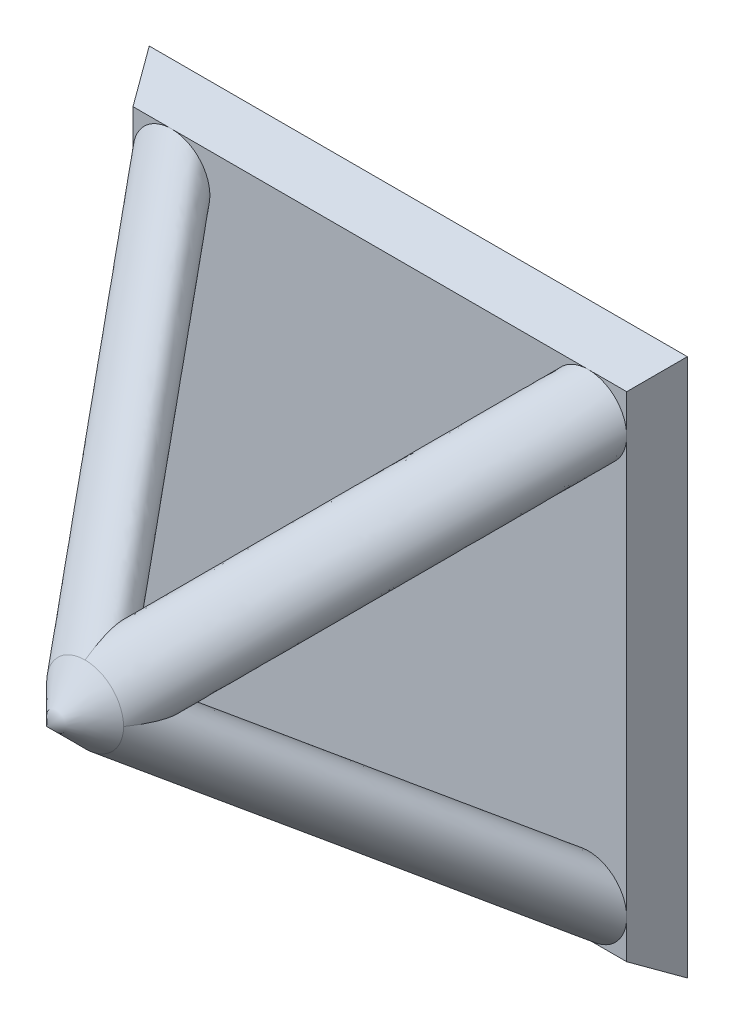
SolidWorks part; units mm, degrees
ref_plane "Front" through (0, 0, 0) normal (0, 0, 1) x (1, 0, 0)
ref_plane "Top" through (0, 0, 0) normal (0, 1, 0) x (1, 0, 0)
ref_plane "Right" through (0, 0, 0) normal (1, 0, 0) x (0, 0, -1)
sketch "Sketch1" plane through (0, 0, 0) normal (0, 0, 1) x (1, 0, 0)
  line L0 (0, 0) -> (0, 43.0475) construction
  line L1 (-7, 7) -> (7, 7)
  line L2 (-7, 7) -> (-7, -7)
  line L3 (-7, -7) -> (7, -7)
  line L4 (7, 7) -> (7, -7)
  line L5 (0, 0) -> (74.4916, 0) construction
  point P7 (0, 7)
  point P8 (7, 0)
  dimension "D1" = 14
  dimension "D2" = 14
extrude "Boss-Extrude1" add sketch "Sketch1" along normal blind 1 draft 30
sketch "Sketch2" plane through (0, 0, 1) normal (0, 0, 1) x (1, 0, 0)
  line L0 (6.4226, -6.4226) -> (6.4226, 6.4226) construction
  line L1 (6.4226, 6.4226) -> (-6.4226, 6.4226) construction
  circle A0 centre (5.4226, 5.4226) radius 1
  dimension "D1" = 2
ref_plane "Plane1" through (0, 0, 0) normal (0.7071, -0.7071, 0) x (0, 0, -1)
sketch "Sketch3" plane through (0, 0, 0) normal (0.7071, -0.7071, 0) x (0, 0, -1)
  line L0 (-1, 7.6688) -> (-8.6688, 0)
  line L1 (0, 0) -> (-12.2099, 0) construction
sweep "Sweep1" add profiles "Sketch2" path "Sketch3"
ref_axis "Axis1" through (0, 0, -4.2318) along (0, 0, 1)
pattern_circular "CirPattern1" count 4 over 360 about axis through (0, 0, -4.2318) along (0, 0, 1) of "Sweep1"
sketch "Sketch4" plane through (0, 0, 8.6688) normal (0, 0, 1) x (1, 0, 0)
  circle A0 centre (0, 0) radius 1
extrude "Boss-Extrude2" add sketch "Sketch4" along normal blind 10 draft 45
